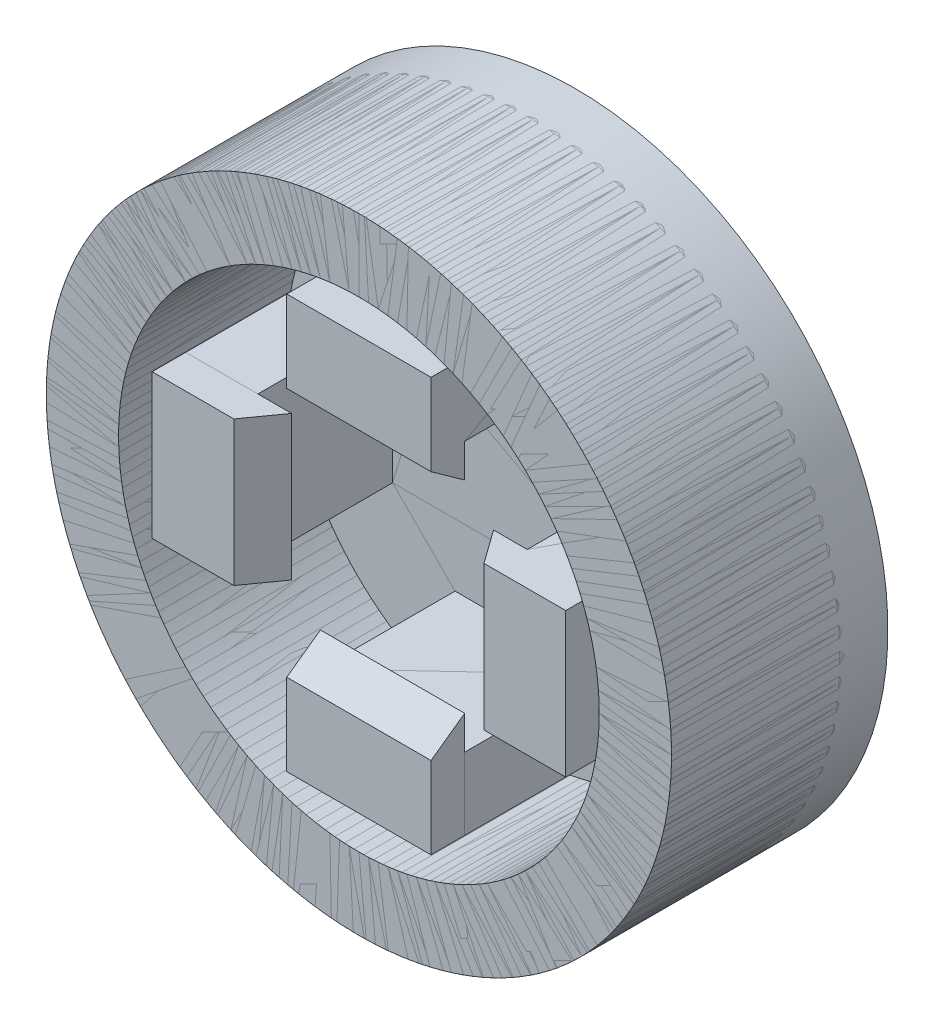
SolidWorks part; units mm, degrees
ref_plane "Plan de face" through (0, 0, 0) normal (0, 0, 1) x (1, 0, 0)
ref_plane "Plan de dessus" through (0, 0, 0) normal (0, 1, 0) x (1, 0, 0)
ref_plane "Plan de droite" through (0, 0, 0) normal (1, 0, 0) x (0, 0, -1)
sketch "Esquisse1" plane through (0, 0, 0) normal (0, 0, 1) x (1, 0, 0)
  circle A0 centre (0, 0) radius 6.5
  dimension "D1" = 13
extrude "Boss.-Extru.1" add sketch "Esquisse1" along normal blind 1
sketch "Esquisse2" plane through (0, 0, 1) normal (0, 0, 1) x (1, 0, 0)
  circle A0 centre (0, 0) radius 6.5
  circle A2 centre (0, 0) radius 6.5 construction
  circle A3 centre (0, 0) radius 5
  dimension "D1" = 10
extrude "Boss.-Extru.2" add sketch "Esquisse2" along normal blind 3.5
sketch "Esquisse3" plane through (0, 0, 1) normal (0, 0, 1) x (1, 0, 0)
  line L0 (0, 0) -> (0, 3.55) construction
  line L1 (2.8, -1.5) -> (4.3, -1.5)
  line L2 (-1.5, 2.8) -> (1.5, 2.8)
  line L3 (-1.5, 2.8) -> (-1.5, 4.3)
  line L4 (-1.5, 4.3) -> (1.5, 4.3)
  line L5 (1.5, 2.8) -> (1.5, 4.3)
  line L6 (-1.5, 2.8) -> (1.5, 4.3) construction
  line L7 (-1.5, 4.3) -> (1.5, 2.8) construction
  line L8 (4.3, 1.5) -> (4.3, -1.5)
  line L9 (2.8, 1.5) -> (4.3, 1.5)
  line L10 (2.8, 1.5) -> (2.8, -1.5)
  line L11 (-1.5, -2.8) -> (-1.5, -4.3)
  line L12 (1.5, -4.3) -> (-1.5, -4.3)
  line L13 (1.5, -2.8) -> (1.5, -4.3)
  line L14 (1.5, -2.8) -> (-1.5, -2.8)
  line L15 (-2.8, 1.5) -> (-4.3, 1.5)
  line L16 (-4.3, -1.5) -> (-4.3, 1.5)
  line L17 (-2.8, -1.5) -> (-4.3, -1.5)
  line L18 (-2.8, -1.5) -> (-2.8, 1.5)
  circle A0 centre (0, 0) radius 3.55 construction
  circle A1 centre (0, 0) radius 3.55 construction
  circle A2 centre (0, 0) radius 3.55 construction
  circle A3 centre (0, 0) radius 3.55 construction
  point P26 (0, 0)
  dimension "D1" = 7.1
  dimension "D2" = 1.5
  dimension "D3" = 3
  dimension "D4" = 4
extrude "Boss.-Extru.3" add sketch "Esquisse3" along normal blind 2.8
sketch "Esquisse4" plane through (-1.5, 0, 0) normal (-1, 0, 0) x (0, 0, 1)
  line L0 (3.8, 4.3) -> (3.8, 2.1)
  line L1 (3.8, 2.1) -> (4.5, 2.6)
  line L2 (4.5, 2.6) -> (4.5, 4.3)
  line L3 (4.5, 4.3) -> (3.8, 4.3)
  dimension "D1" = 0.7
  dimension "D2" = 0.5
  dimension "D3" = 2.2
extrude "Boss.-Extru.4" add sketch "Esquisse4" against normal up to surface (3 mm away) up to face at (1.5, 3.55, 2.4)
pattern_circular "Répétition circulaire10" count 4 over 360 about axis through (0, 0, 0) along (0, 0, 1) of bodies 104
sketch "Esquisse5" plane through (0, 0, 0) normal (1, 0, 0) x (0, 0, -1)
  line L0 (0, -6.5) -> (-1, -6.5)
  line L1 (-4.5, -6.5) -> (0, -6.5) construction
  line L2 (0, -6.5) -> (0, 6.5) construction
  line L3 (0, -5.5) -> (0, -6.5)
  arc A0 (-1, -6.5) -> (0, -5.5) centre (-1, -5.5) ccw
  dimension "D1" = 1
revolve "Enlèvement de matière-Révolution1" cut sketch "Esquisse5" angle 360 about axis through (0, 0, 1) along (0, 0, -1)
